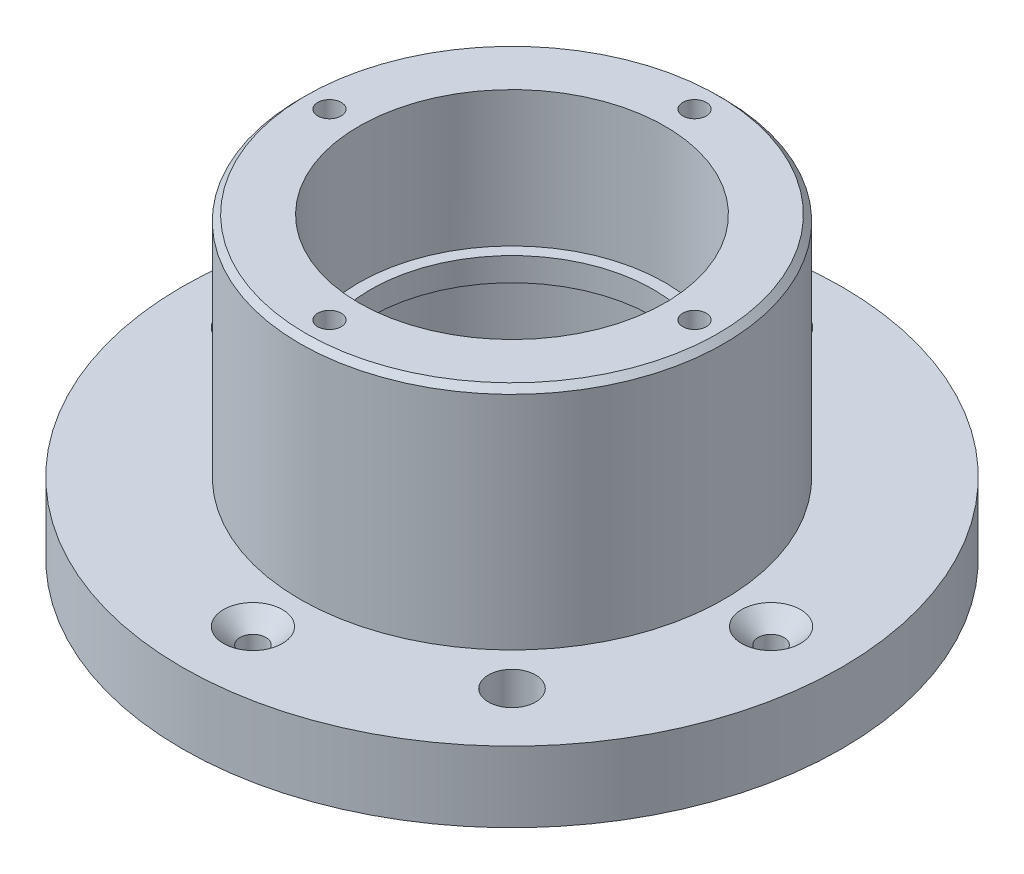
SolidWorks part; units mm, degrees
material "ABS"
ref_plane "Спереди" through (0, 0, 0) normal (0, 0, 1) x (1, 0, 0)
ref_plane "Сверху" through (0, 0, 0) normal (0, 1, 0) x (1, 0, 0)
ref_plane "Справа" through (0, 0, 0) normal (1, 0, 0) x (0, 0, -1)
sketch "Эскиз1" plane through (0, 0, 0) normal (0, 1, 0) x (1, 0, 0)
  circle A0 centre (0, 0) radius 26
  dimension "D1" = 52
extrude "Бобышка-Вытянуть1" add sketch "Эскиз1" along normal blind 4
sketch "Эскиз2" plane through (0, 4, 0) normal (0, 1, 0) x (1, 0, 0)
  circle A0 centre (0, 0) radius 18
  dimension "D1" = 36
extrude "Бобышка-Вытянуть2" add sketch "Эскиз2" along normal blind 19.3
sketch "Эскиз3" plane through (0, 23.3, 0) normal (0, 1, 0) x (1, 0, 0)
  circle A0 centre (0, 0) radius 13
  dimension "D1" = 26
extrude "Вырез-Вытянуть1" cut sketch "Эскиз3" along direction (0, 1, 0) on the side against the normal offset from surface (10.3 mm away) 13
sketch "Эскиз4" plane through (0, 4, 0) normal (0, 1, 0) x (1, 0, 0)
  circle A0 centre (0, 0) radius 22 construction
  circle A1 centre (-22, 0) radius 2.2
  circle A2 centre (0, 22) radius 2.2
  circle A3 centre (22, 0) radius 2.2
  circle A4 centre (0, -22) radius 2.2
  point P14 (0, 0)
  dimension "D1" = 44
  dimension "D2" = 4.4
  dimension "D3" = 4
sketch "Эскиз6" plane through (0, 13, 0) normal (0, 1, 0) x (1, 0, 0)
  circle A0 centre (0, 0) radius 13
  dimension "D1" = 26
extrude "Вырез-Вытянуть4" cut sketch "Эскиз6" against normal through all
sketch "Эскиз7" plane through (0, 23.3, 0) normal (0, 1, 0) x (1, 0, 0)
  circle A0 centre (0, 0) radius 15.5 construction
  circle A1 centre (-15.5, 0) radius 1
  circle A2 centre (0, 15.5) radius 1
  circle A3 centre (15.5, 0) radius 1
  circle A4 centre (0, -15.5) radius 1
  point P14 (0, 0)
  dimension "D1" = 31
  dimension "D2" = 2
extrude "Вырез-Вытянуть5" cut sketch "Эскиз7" against normal blind 5
sketch "Эскиз8" plane through (0, 4, 0) normal (0, 1, 0) x (1, 0, 0)
  circle A0 centre (0, 0) radius 26
  circle A1 centre (0, 0) radius 28
  dimension "D1" = 56
  dimension "D2" = 52
extrude "Бобышка-Вытянуть3" add sketch "Эскиз8" against normal blind 6
chamfer "Фаска1" distance 0.5 angle 45 1 edges at (0, -2, 26)
chamfer "Фаска2" distance 0.5 angle 45 1 edges at (0, 23.3, 18)
ref_axis "Ось1" through (0, -20.7688, 22) along (0, 1, 0)
sketch "Эскиз9" plane through (0, 0, 0) normal (1, 0, 0) x (0, 0, -1)
  line L1 (-22, -20.7688) -> (-22, 30.1347) construction
  line L2 (-20.9, 2.648) -> (-19.5, 4)
  line L3 (22, 4) -> (-22, 4) construction
  line L4 (-19.5, 4) -> (-22, 4)
  line L5 (-19.8, 4) -> (-24.2, 4) construction
  line L6 (-22, 2.648) -> (-22, 4)
  line L7 (-20.9, 2.648) -> (-20.9, -2)
  line L8 (-28, -2) -> (28, -2) construction
  line L9 (-20.9, -2) -> (-22, -2)
  line L10 (-22, -2) -> (-22, 2.648)
  dimension "D1" = 1.1
  dimension "D2" = 2.5
  dimension "D3" = 46
revolve "Вырез-Повернуть2" cut sketch "Эскиз9" angle 360 about axis through (0, -20.7688, 22) along (0, 1, 0)
pattern_circular "Круговой массив1" count 4 over 360 about axis through (0, 0, 0) along (0, 1, 0) of "Вырез-Повернуть2"
sketch "Эскиз10" plane through (0, 0, 0) normal (0, -1, 0) x (1, 0, 0)
  circle A0 centre (0, 0) radius 15
  dimension "D1" = 30
extrude "Вырез-Вытянуть7" cut sketch "Эскиз10" against normal blind 11.8 contours A0
sketch "Эскиз11" plane through (0, 11.8, 0) normal (0, -1, 0) x (1, 0, 0)
  circle A2 centre (0, 0) radius 15
  circle A3 centre (0, 0) radius 12
  dimension "D1" = 24
extrude "Бобышка-Вытянуть4" add sketch "Эскиз11" along normal blind 2
sketch "Эскиз12" plane through (0, 4, 0) normal (0, 1, 0) x (1, 0, 0)
  line L0 (0, 0) -> (24.2478, -24.2478) construction
  line L1 (0, 0) -> (0, 9.2469) construction
  circle A0 centre (15.5563, -15.5563) radius 2
  dimension "D2" = 4
  dimension "D1" = 135
  dimension "D3" = 22
extrude "Вырез-Вытянуть8" cut sketch "Эскиз12" against normal blind 10
